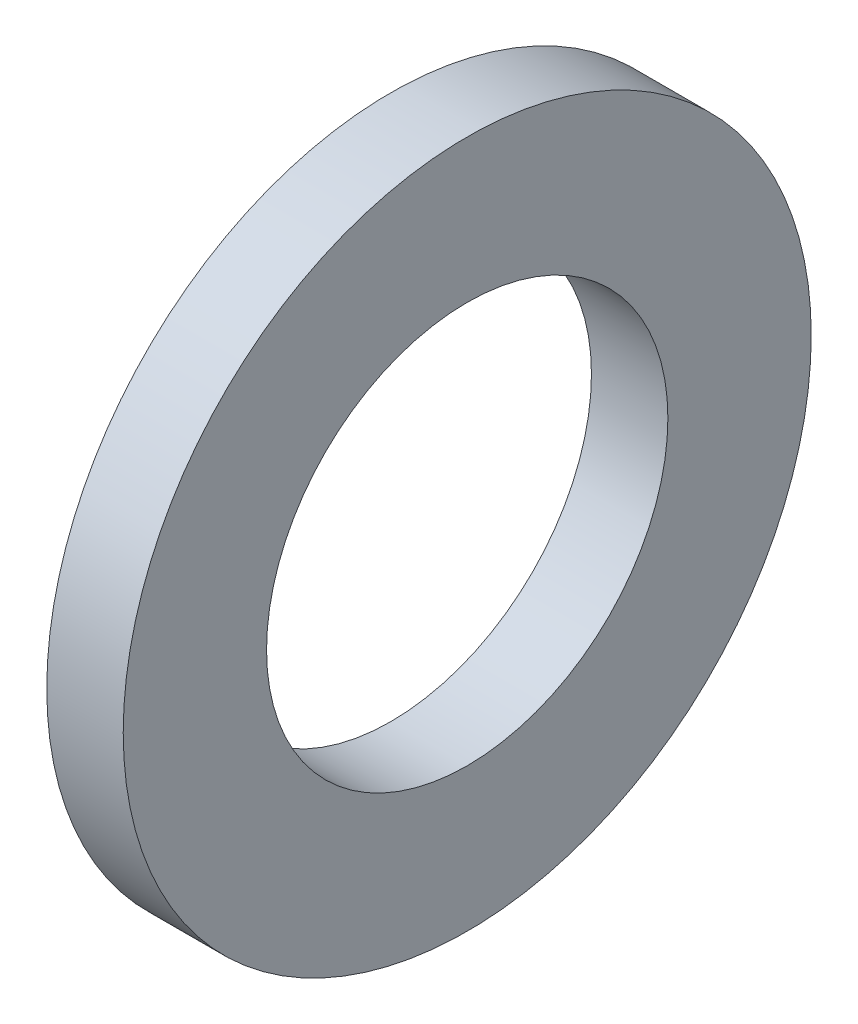
SolidWorks part; units mm, degrees
ref_plane "Plane1" through (0, 0, 0) normal (0, 0, 1) x (1, 0, 0)
ref_plane "Plane2" through (0, 0, 0) normal (0, 1, 0) x (1, 0, 0)
ref_plane "Plane3" through (0, 0, 0) normal (1, 0, 0) x (0, 0, -1)
sketch "Sketch1" plane through (0, 0, 0) normal (0, 0, 1) x (1, 0, 0)
  line L0 (-34.925, 0) -> (9.525, 0) construction
  line L1 (0, 5.25) -> (0, 9)
  line L2 (0, 9) -> (-2, 9)
  line L3 (-2, 9) -> (-2, 5.25)
  line L4 (-2, 5.25) -> (0, 5.25)
  dimension "Thickness" = 2
  dimension "Inside_dia" = 10.5
  dimension "Outside_dia" = 18
revolve "Base-Revolve" add sketch "Sketch1" angle 360 about L0
